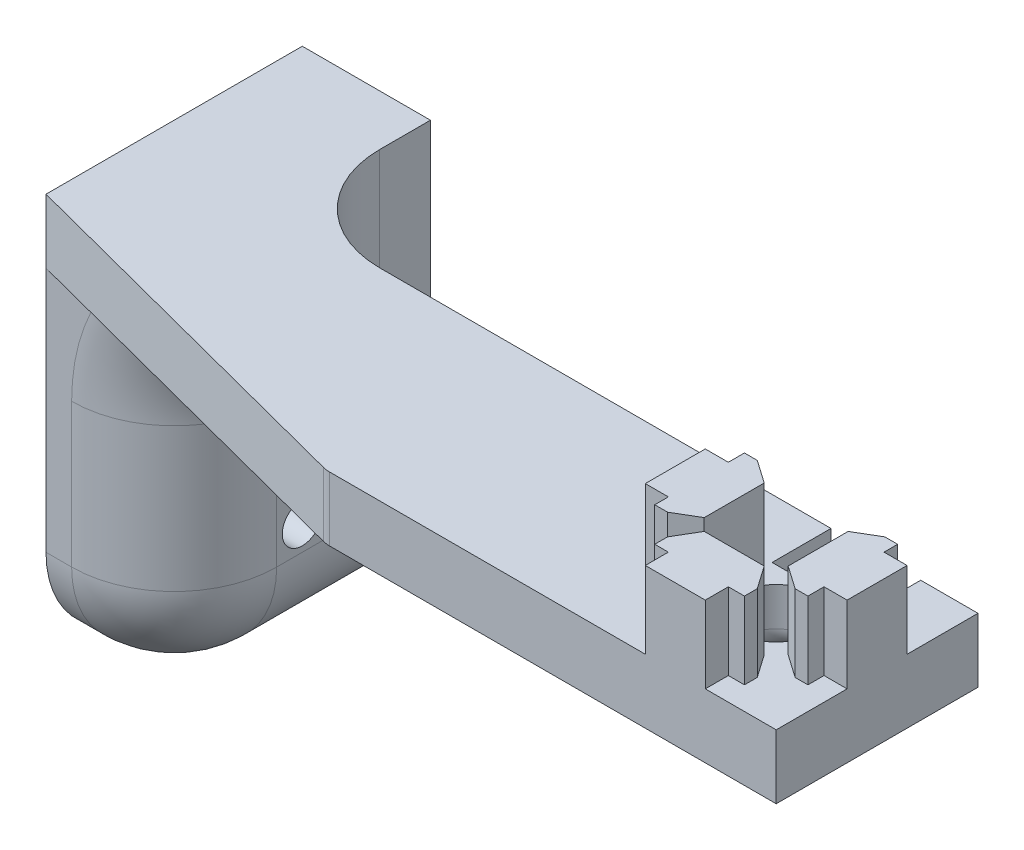
SolidWorks part; units mm, degrees
ref_plane "Front Plane" through (0, 0, 0) normal (0, 0, 1) x (1, 0, 0)
ref_plane "Top Plane" through (0, 0, 0) normal (0, 1, 0) x (1, 0, 0)
ref_plane "Right Plane" through (0, 0, 0) normal (1, 0, 0) x (0, 0, -1)
sketch "Sketch1" plane through (0, 0, 0) normal (0, 1, 0) x (1, 0, 0)
  line L0 (-2.9718, 10) -> (-2.9718, 7.714)
  line L1 (-10, 10) -> (10, 10)
  line L2 (-10, 10) -> (-10, -10)
  line L3 (-10, -10) -> (10, -10)
  line L4 (10, 10) -> (10, -10)
  line L5 (-10, 10) -> (10, -10) construction
  line L6 (-10, -10) -> (10, 10) construction
  line L7 (-2.9718, 10) -> (2.9718, 10) construction
  line L8 (-2.9718, 10) -> (-2.9718, 4.158) construction
  line L9 (-2.9718, 4.158) -> (2.9718, 4.158) construction
  line L10 (2.9718, 10) -> (2.9718, 4.158) construction
  line L11 (-4.5679, 7.714) -> (4.3221, 7.714) construction
  line L12 (-4.5679, 7.714) -> (-4.5679, 6.444) construction
  line L13 (-4.5679, 6.444) -> (4.3221, 6.444) construction
  line L14 (4.3221, 7.714) -> (4.3221, 6.444) construction
  line L15 (-4.5679, 7.714) -> (4.3221, 6.444) construction
  line L16 (-4.5679, 6.444) -> (4.3221, 7.714) construction
  line L17 (-2.9718, 7.714) -> (-4.5679, 7.714)
  line L18 (-4.5679, 7.714) -> (-4.5679, 6.444)
  line L19 (-4.5679, 6.444) -> (-2.9718, 4.158)
  line L20 (-2.9718, 4.158) -> (2.9718, 4.158)
  line L21 (2.9718, 4.158) -> (4.3221, 6.444)
  line L22 (4.3221, 6.444) -> (4.3221, 7.714)
  line L23 (4.3221, 7.714) -> (2.9718, 7.714)
  line L24 (2.9718, 7.714) -> (2.9718, 10)
  line L25 (2.9718, 10) -> (-2.9718, 10)
  line L26 (4.158, -2.9718) -> (4.158, 2.9718)
  line L27 (4.158, 2.9718) -> (6.444, 4.3221)
  line L28 (6.444, 4.3221) -> (7.714, 4.3221)
  line L29 (7.714, 4.3221) -> (7.714, 2.9718)
  line L30 (7.714, 2.9718) -> (10, 2.9718)
  line L31 (10, -2.9718) -> (10, 2.9718) construction
  line L32 (10, 2.9718) -> (10, -2.9718)
  line L33 (10, -2.9718) -> (7.714, -2.9718)
  line L34 (7.714, -2.9718) -> (7.714, -4.5679)
  line L35 (7.714, -4.5679) -> (6.444, -4.5679)
  line L36 (6.444, -4.5679) -> (4.158, -2.9718)
  line L37 (2.9718, -10) -> (-2.9718, -10) construction
  line L38 (4.5679, -6.444) -> (2.9718, -4.158)
  line L39 (4.5679, -7.714) -> (4.5679, -6.444)
  line L40 (2.9718, -7.714) -> (4.5679, -7.714)
  line L41 (2.9718, -10) -> (2.9718, -7.714)
  line L42 (-2.9718, -10) -> (2.9718, -10)
  line L43 (-2.9718, -7.714) -> (-2.9718, -10)
  line L44 (-4.3221, -7.714) -> (-2.9718, -7.714)
  line L45 (-4.3221, -6.444) -> (-4.3221, -7.714)
  line L46 (-2.9718, -4.158) -> (-4.3221, -6.444)
  line L47 (2.9718, -4.158) -> (-2.9718, -4.158)
  line L48 (-10, 2.9718) -> (-10, -2.9718) construction
  line L49 (-10, -2.9718) -> (-10, 2.9718)
  line L50 (-7.714, -2.9718) -> (-10, -2.9718)
  line L51 (-7.714, -4.3221) -> (-7.714, -2.9718)
  line L52 (-6.444, -4.3221) -> (-7.714, -4.3221)
  line L53 (-4.158, -2.9718) -> (-6.444, -4.3221)
  line L54 (-4.158, 2.9718) -> (-4.158, -2.9718)
  line L55 (-6.444, 4.5679) -> (-4.158, 2.9718)
  line L56 (-7.714, 4.5679) -> (-6.444, 4.5679)
  line L57 (-7.714, 2.9718) -> (-7.714, 4.5679)
  line L58 (-10, 2.9718) -> (-7.714, 2.9718)
  point P0 (0, 0)
  point P12 (0, 4.158)
  point P13 (-0.1229, 7.079)
  dimension "D1" = 20
  dimension "D2" = 20
  dimension "D4" = 5.9436
  dimension "D5" = 10
  dimension "D6" = 5.842
  dimension "D7" = 2.286
  dimension "D8" = 3.556
  dimension "D9" = 8.89
extrude "Boss-Extrude1" add sketch "Sketch1" along normal blind 7.62 contours L23 L24 L1 L0 L17 L18 L19 L20 L21 L22 | L26 L27 L28 L29 L30 L32 L33 L34 L35 L36 | L49 L58 L57 L56 L55 L54 L53 L52 L51 L50 | L38 L47 L46 L45 L44 L43 L42 L41 L40 L39
sketch "Sketch2" plane through (0, 0, 0) normal (0, -1, 0) x (1, 0, 0)
  line L1 (10, -10) -> (-72.1538, -10)
  line L2 (10, -10) -> (10, 10)
  line L3 (10, 10) -> (-72.1538, 10)
  line L4 (-72.1538, -10) -> (-72.1538, 10)
  line L5 (10, -10) -> (-72.1538, 10) construction
  line L6 (10, 10) -> (-72.1538, -10) construction
  line L7 (-2.9718, -10) -> (2.9718, -10) construction
  line L8 (10, -2.9718) -> (10, 2.9718) construction
  dimension "D1" = 82.1538
  dimension "D2" = 20
  dimension "D3" = 0
  dimension "D4" = 0
extrude "Boss-Extrude2" add sketch "Sketch2" along normal blind 6.35
sketch "Sketch4" plane through (0, -6.35, 0) normal (0, -1, 0) x (-1, 0, 0)
  line L0 (72.1538, 10) -> (72.1538, -0.2108) construction
  line L1 (72.1538, -10) -> (72.1538, 10) construction
  line L2 (72.1538, -10) -> (34.6126, -10)
  line L3 (-10, -10) -> (72.1538, -10) construction
  line L4 (34.6126, -10) -> (72.1538, -0.2108)
  line L5 (72.1538, -0.2108) -> (72.1538, -10)
  dimension "D1" = 10.2108
  dimension "D2" = 37.5412
extrude "Cut-Extrude1" cut sketch "Sketch4" against normal through all
fillet "Fillet1" radius 2.54 1 edges at (-34.6126, -3.175, 10)
sketch "Sketch13" plane through (0, 0, 0) normal (0, 1, 0) x (1, 0, 0)
  line L1 (4.158, 2.9718) -> (-4.158, 2.9718) construction
  line L2 (4.158, 2.9718) -> (4.158, -2.9718) construction
  line L3 (4.158, -2.9718) -> (-4.158, -2.9718) construction
  line L4 (-4.158, 2.9718) -> (-4.158, -2.9718) construction
  circle A0 centre (0, 0) radius 3.5
  dimension "D1" = 7
extrude "Cut-Extrude5" cut sketch "Sketch13" against normal through all
fillet "Fillet6" radius 2.54 1 edges at (0, -6.35, 3.5)
sketch "Sketch14" plane through (0, 7.62, 0) normal (0, 1, 0) x (1, 0, 0)
  line L5 (4.3221, 10) -> (-4.5679, 10)
  line L6 (4.3221, 10) -> (4.3221, 4.158)
  line L7 (4.3221, 4.158) -> (-4.5679, 4.158)
  line L8 (-4.5679, 10) -> (-4.5679, 4.158)
  line L18 (4.3221, 6.444) -> (4.3221, 7.714) construction
  line L19 (-4.5679, 7.714) -> (-4.5679, 6.444) construction
  dimension "D5" = 0
  dimension "D6" = 0
extrude "Cut-Extrude6" cut sketch "Sketch14" against normal through all
sketch "Sketch15" plane through (-72.1538, 0, 0) normal (-1, 0, 0) x (0, 0, 1)
  line L0 (0.2108, -6.35) -> (-10, -6.35) construction
  line L10 (0.2108, 0) -> (-25.1892, 0)
  line L11 (0.2108, 0) -> (0.2108, -40.894)
  line L12 (0.2108, -40.894) -> (-25.1892, -40.894)
  line L13 (-25.1892, 0) -> (-25.1892, -40.894)
  dimension "D1" = 34.544
  dimension "D2" = 25.4
extrude "Boss-Extrude3" add sketch "Sketch15" against normal blind 12.7
fillet "Fillet15" radius 10.16 1 edges at (-59.4538, -6.35, -4.8946)
fillet "Fillet16" radius 10.16 1 edges at (-59.4538, -8.255, -10)
fillet "Fillet17" radius 10.16 1 edges at (-59.4538, -40.894, -12.4892)
fillet "Fillet18" radius 10.16 4 edges at (-70.8838, -40.894, 0.2108) (-62.4296, -37.9182, 0.2108) (-56.478, -9.3258, 0.2108) (-59.4538, -23.622, 0.2108)
sketch "Sketch18" plane through (-72.1538, 0, 0) normal (-1, 0, 0) x (0, 0, 1)
  line L1 (-25.1892, -40.894) -> (-12.4892, -40.894) construction
  line L2 (-25.1892, -40.894) -> (-25.1892, -28.194) construction
  line L3 (-25.1892, -28.194) -> (-12.4892, -28.194) construction
  line L4 (-12.4892, -40.894) -> (-12.4892, -28.194) construction
  circle A0 centre (-12.4892, -28.194) radius 1.9844
  dimension "D3" = 3.9688
  dimension "D1" = 12.7
  dimension "D2" = 12.7
extrude "Cut-Extrude9" cut sketch "Sketch18" against normal up to surface (12.7 mm away) up to face at (-59.4538, -15.748, -18.4328)
